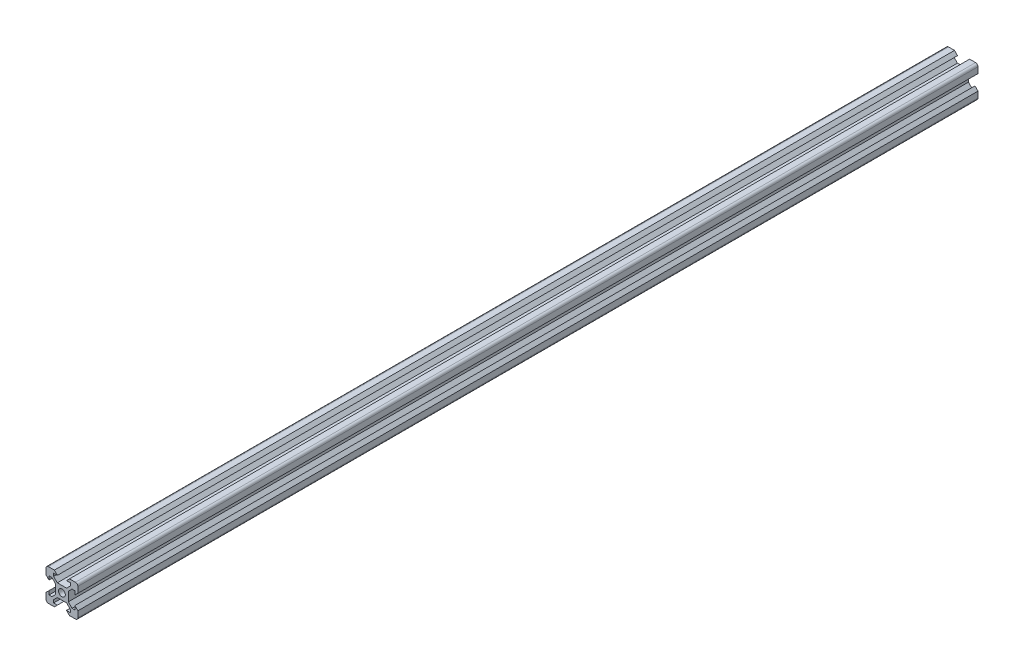
SolidWorks part; units mm, degrees
ref_plane "Front Plane" through (0, 0, 0) normal (0, 0, 1) x (1, 0, 0)
ref_plane "Top Plane" through (0, 0, 0) normal (0, 1, 0) x (1, 0, 0)
ref_plane "Right Plane" through (0, 0, 0) normal (1, 0, 0) x (0, 0, -1)
sketch "Sketch1" plane through (0, 0, 0) normal (0, 0, 1) x (1, 0, 0)
  line L0 (15.6876, 55.3211) -> (115.0437, 55.3211) construction
  line L1 (8.1, 5.225) -> (8.1, 2.85)
  line L2 (-8.5, 10) -> (-4.75, 10)
  line L3 (-10, 8.5) -> (-10, 4.75)
  line L4 (-8.5, -10) -> (-4.75, -10)
  line L5 (10, 8.5) -> (10, 4.75)
  line L6 (6.325, 5.225) -> (4, 2.9)
  line L7 (-8.1, -2.85) -> (-8.1, -5.225)
  line L8 (-2.9, 4) -> (2.9, 4)
  line L9 (-4, 2.9) -> (-4, -2.9)
  line L10 (-2.9, -4) -> (2.9, -4)
  line L11 (4, 2.9) -> (4, -2.9)
  line L12 (2.85, -8.1) -> (5.225, -8.1)
  line L13 (-5.225, -8.1) -> (-2.85, -8.1)
  line L14 (5.225, 6.325) -> (2.9, 4)
  line L17 (-10, 4.75) -> (-8.1, 2.85)
  line L20 (4.75, -10) -> (8.5, -10)
  line L22 (-10, -4.75) -> (-10, -8.5)
  line L23 (10, -4.75) -> (10, -8.5)
  line L24 (-10, -4.75) -> (-8.1, -2.85)
  line L25 (-4.75, -10) -> (-2.85, -8.1)
  line L26 (4.75, -10) -> (2.85, -8.1)
  line L27 (10, -4.75) -> (8.1, -2.85)
  line L28 (10, 4.75) -> (8.1, 2.85)
  line L29 (-4.75, 10) -> (-2.85, 8.1)
  line L30 (4.75, 10) -> (2.85, 8.1)
  line L31 (8.1, -2.85) -> (8.1, -5.225)
  line L32 (6.325, -5.225) -> (8.1, -5.225)
  line L33 (5.225, -6.325) -> (5.225, -8.1)
  line L34 (4.75, 10) -> (8.5, 10)
  line L35 (2.85, 8.1) -> (5.225, 8.1)
  line L36 (10, -10) -> (10.975, -10.975) construction
  line L37 (-5.225, 8.1) -> (-2.85, 8.1)
  line L38 (-8.1, -5.225) -> (-6.325, -5.225)
  line L39 (-5.225, 6.325) -> (-2.9, 4)
  line L40 (-8.1, 5.225) -> (-8.1, 2.85)
  line L41 (-5.225, -6.325) -> (-5.225, -8.1)
  line L42 (-6.325, 5.225) -> (-4, 2.9)
  line L46 (-8.1, 5.225) -> (-6.325, 5.225)
  line L47 (-5.225, 8.1) -> (-5.225, 6.325)
  line L52 (8.1, 5.225) -> (6.325, 5.225)
  line L53 (5.225, 8.1) -> (5.225, 6.325)
  line L63 (4, -2.9) -> (6.325, -5.225)
  line L66 (2.9, -4) -> (5.225, -6.325)
  line L67 (-2.9, -4) -> (-5.225, -6.325)
  line L70 (-4, -2.9) -> (-6.325, -5.225)
  arc A0 (-8.5, -10) -> (-10, -8.5) centre (-8.5, -8.5) cw
  arc A1 (8.5, -10) -> (10, -8.5) centre (8.5, -8.5) ccw
  arc A2 (10, 8.5) -> (8.5, 10) centre (8.5, 8.5) ccw
  arc A3 (-8.5, 10) -> (-10, 8.5) centre (-8.5, 8.5) ccw
  circle A4 centre (0, 0) radius 2.125
  point P2 (0, 0)
  point P8 (0, 0)
  point P14 (-10, -10)
  point P20 (0, 0)
  point P49 (10, 10)
  point P52 (-10, 10)
extrude "Boss-Extrude1" add sketch "Sketch1" along normal blind 565
